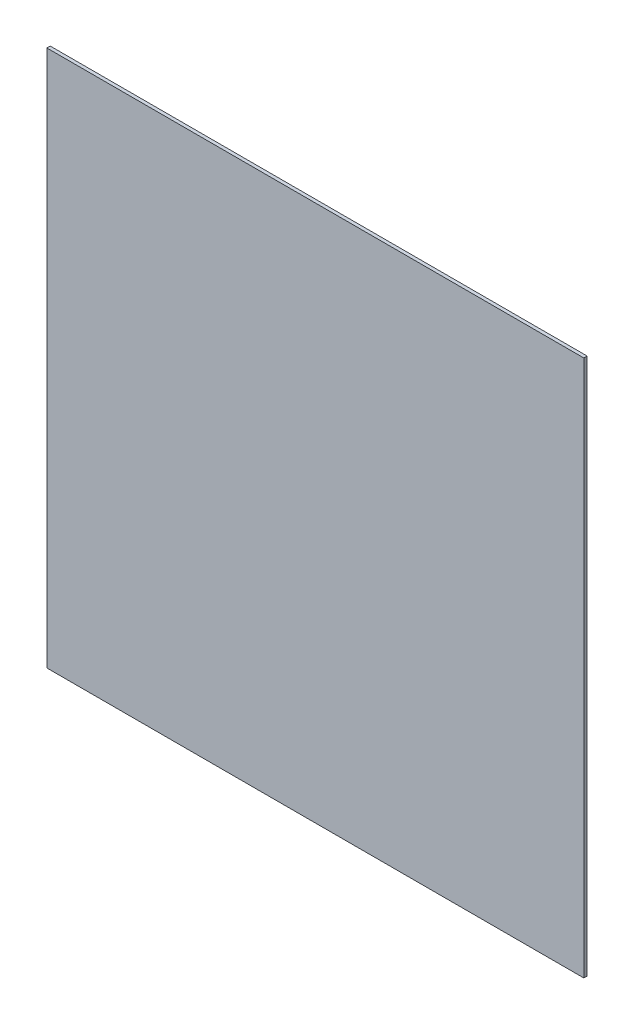
SolidWorks part; units mm, degrees
material "Silicon"
ref_plane "Front Plane" through (0, 0, 0) normal (0, 0, 1) x (1, 0, 0)
ref_plane "Top Plane" through (0, 0, 0) normal (0, 1, 0) x (1, 0, 0)
ref_plane "Right Plane" through (0, 0, 0) normal (1, 0, 0) x (0, 0, -1)
sketch "Sketch1" plane through (0, 0, 0) normal (0, 0, 1) x (1, 0, 0)
  line L1 (-160, -160) -> (160, -160)
  line L2 (-160, -160) -> (-160, 160)
  line L3 (-160, 160) -> (160, 160)
  line L4 (160, -160) -> (160, 160)
  line L5 (-160, -160) -> (160, 160) construction
  line L6 (-160, 160) -> (160, -160) construction
  point P0 (0, 0)
  dimension "D1" = 320
  dimension "D2" = 320
extrude "Boss-Extrude1" add sketch "Sketch1" along normal blind 3.5
chamfer "Chamfer1" distance 1.5 angle 45 4 edges at (0, 160, 0) (-160, 0, 0) (0, -160, 0) (160, 0, 0)
